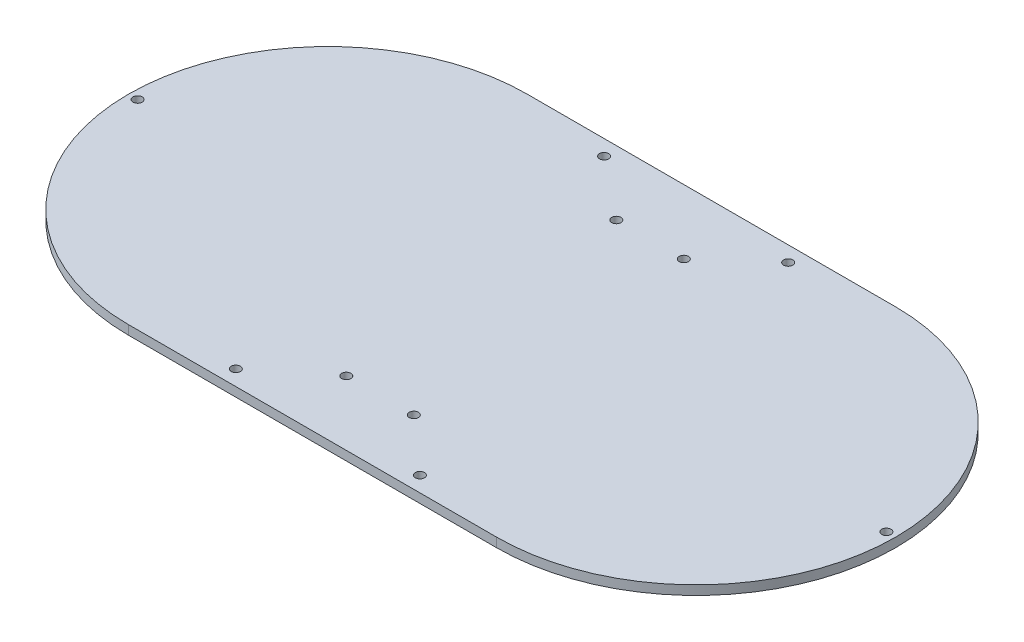
SolidWorks part; units mm, degrees
ref_plane "前视基准面" through (0, 0, 0) normal (0, 0, 1) x (1, 0, 0)
ref_plane "上视基准面" through (0, 0, 0) normal (0, 1, 0) x (1, 0, 0)
ref_plane "右视基准面" through (0, 0, 0) normal (1, 0, 0) x (0, 0, -1)
sketch "草图1" plane through (0, 0, 0) normal (0, 1, 0) x (1, 0, 0)
  line L0 (0, 0) -> (0, 89.0672) construction
  line L1 (-60, 0) -> (60, 0) construction
  line L2 (-60, 70) -> (60, 70) construction
  line L3 (-60, -70) -> (60, -70) construction
  line L4 (-90, 51.9615) -> (-60, 0) construction
  line L5 (-90, -51.9615) -> (-60, 0) construction
  line L6 (90, -51.9615) -> (60, 0) construction
  line L7 (90, 51.9615) -> (60, 0) construction
  line L8 (0, 0) -> (76.6344, 0) construction
  line L9 (-49.5811, 59.0885) -> (-60, 0) construction
  line L10 (-116.3816, -20.5212) -> (-60, 0) construction
  line L11 (-14.0373, -38.5673) -> (-60, 0) construction
  line L12 (-60, 65) -> (60, 65)
  line L13 (-60, -65) -> (60, -65)
  arc A2 (-60, 70) -> (-60, -70) centre (-60, 0) ccw construction
  arc A3 (60, -70) -> (60, 70) centre (60, 0) ccw construction
  circle A4 centre (0, 0) radius 1.5 construction
  circle A5 centre (-90, 51.9615) radius 1.5 construction
  circle A6 centre (-90, -51.9615) radius 1.5 construction
  circle A7 centre (90, -51.9615) radius 1.5 construction
  circle A8 centre (90, 51.9615) radius 1.5 construction
  circle A9 centre (0, 0) radius 1.5 construction
  circle A10 centre (-122, 0) radius 1.5
  circle A11 centre (122, 0) radius 1.5
  circle A12 centre (-30, 60) radius 1.5
  circle A13 centre (30, 60) radius 1.5
  circle A14 centre (30, -60) radius 1.5
  circle A15 centre (-30, -60) radius 1.5
  arc A22 (60, -65) -> (60, 65) centre (60, 0) ccw
  arc A23 (-60, 65) -> (-60, -65) centre (-60, 0) ccw
  point P1 (0, 0)
  point P7 (0, 0)
  dimension "D3" = 5
  dimension "D4" = 3
  dimension "D7" = 3
  dimension "D9" = 3
  dimension "D10" = 60
  dimension "D12" = 3
  dimension "D13" = 62
  dimension "D14" = 62
  dimension "D15" = 3
  dimension "D16" = 3
  dimension "D18" = 60
  dimension "D8" = 120
  dimension "D11" = 120
  dimension "D17" = 30
  dimension "D20" = 60
  dimension "D21" = 80
  dimension "D24" = 120
  dimension "D26" = 60
  dimension "D27" = 120
extrude "凸台-拉伸2" add sketch "草图1" along normal blind 3
sketch "草图2" plane through (0, 3, 0) normal (0, 1, 0) x (1, 0, 0)
  circle A0 centre (-10, 44) radius 1.5
  circle A1 centre (12, 44) radius 1.5
  circle A2 centre (-10, -44) radius 1.5
  circle A3 centre (12, -44) radius 1.5
extrude "切除-拉伸1" cut sketch "草图2" against normal blind 10
